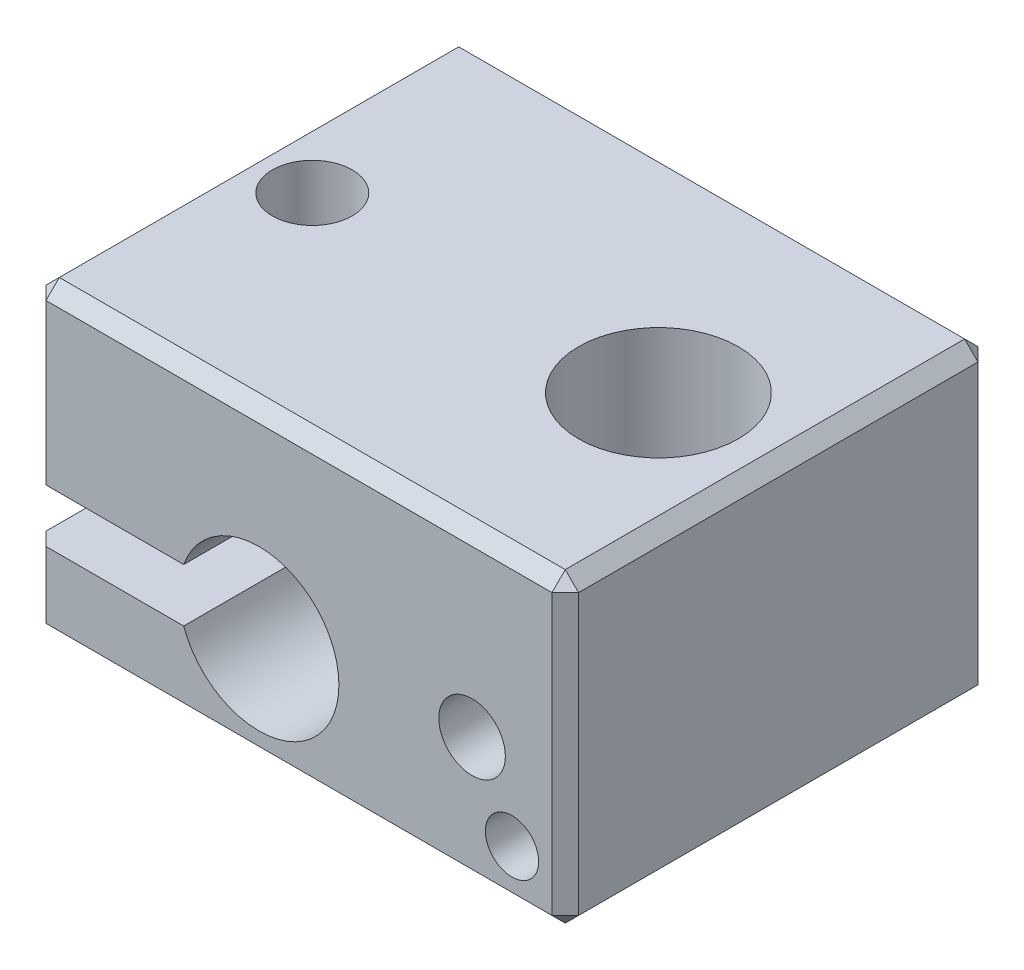
SolidWorks part; units mm, degrees
material "6061-T6 (SS)"
ref_plane "Front Plane" through (0, 0, 0) normal (0, 0, 1) x (1, 0, 0)
ref_plane "Top Plane" through (0, 0, 0) normal (0, 1, 0) x (1, 0, 0)
ref_plane "Right Plane" through (0, 0, 0) normal (1, 0, 0) x (0, 0, -1)
sketch "Sketch1" plane through (0, 0, 0) normal (0, 1, 0) x (1, 0, 0)
  line L0 (0, 0) -> (10, 0) construction
  line L1 (10, 8) -> (-10, 8)
  line L2 (10, 8) -> (10, -8)
  line L3 (10, -8) -> (-10, -8)
  line L4 (-10, 8) -> (-10, -8)
  line L5 (10, 8) -> (-10, -8) construction
  line L6 (10, -8) -> (-10, 8) construction
  line L7 (0, 0) -> (-10, 0) construction
  circle A0 centre (5.5, 0) radius 3
  circle A1 centre (-7.5, 0) radius 1.5
  point P0 (0, 0)
  dimension "D3" = 6
  dimension "D4" = 4.5
  dimension "D5" = 3
  dimension "D6" = 17.5
  dimension "D1" = 16
  dimension "D2" = 20
extrude "Boss-Extrude1" add sketch "Sketch1" along normal blind 11.5
sketch "Sketch2" plane through (0, 0, 8) normal (0, 0, 1) x (1, 0, 0)
  line L0 (-10, 4) -> (-1.5, 4) construction
  line L1 (-10, 11.5) -> (-10, 0) construction
  line L2 (10, 11.5) -> (10, 0) construction
  line L3 (-10, 0) -> (10, 0) construction
  line L4 (-10, 5) -> (-4.3284, 5)
  line L5 (-10, 3) -> (-4.3284, 3)
  line L6 (-10, 5) -> (-10, 3)
  arc A0 (-4.3284, 3) -> (-4.3284, 5) centre (-1.5, 4) ccw
  dimension "D1" = 6
  dimension "D2" = 11.5
  dimension "D3" = 4
  dimension "D4" = 2
  dimension "D5" = 1
extrude "Cut-Extrude1" cut sketch "Sketch2" against normal through all
sketch "Sketch3" plane through (0, 0, 8) normal (0, 0, 1) x (1, 0, 0)
  line L0 (-10, 0) -> (10, 0) construction
  line L1 (10, 11.5) -> (10, 0) construction
  circle A0 centre (6.5, 4.8) radius 1.25
  circle A1 centre (8, 2) radius 1
  dimension "D1" = 2.5
  dimension "D2" = 2
  dimension "D4" = 2
  dimension "D5" = 3.5
  dimension "D6" = 4.8
  dimension "D3" = 2
extrude "Cut-Extrude2" cut sketch "Sketch3" against normal blind 3
chamfer "Chamfer1" distance 0.5 angle 45 14 edges at (10, 11.5, 0) (0, 11.5, 8) (-10, 8.25, 8) (-10, 11.5, 0) (-10, 8.25, -8) (0, 11.5, -8) (-10, 1.5, -8) (-10, 1.5, 8) (10, 5.75, -8) (10, 0, 0) (10, 5.75, 8) (0, 0, -8) (-10, 0, 0) (0, 0, 8)
